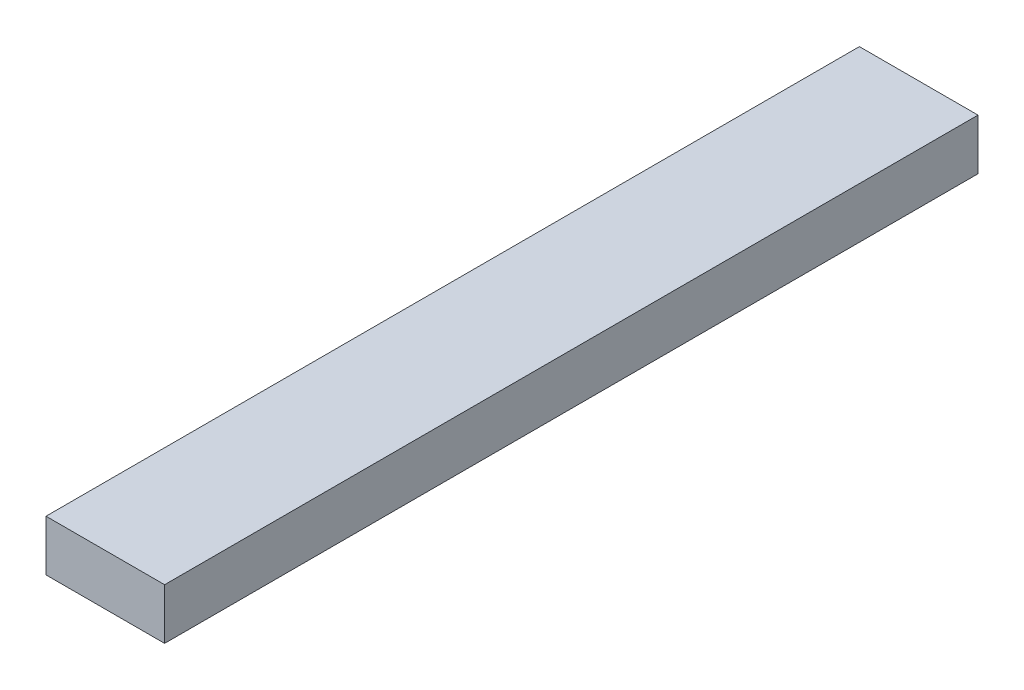
SolidWorks part; units mm, degrees
material "Pine"
ref_plane "Front Plane" through (0, 0, 0) normal (0, 0, 1) x (1, 0, 0)
ref_plane "Top Plane" through (0, 0, 0) normal (0, 1, 0) x (1, 0, 0)
ref_plane "Right Plane" through (0, 0, 0) normal (1, 0, 0) x (0, 0, -1)
sketch "Sketch1" plane through (0, 0, 0) normal (0, 0, 1) x (1, 0, 0)
  line L1 (0, 0) -> (88.9, 0)
  line L2 (0, 0) -> (0, 38.1)
  line L3 (0, 38.1) -> (88.9, 38.1)
  line L4 (88.9, 0) -> (88.9, 38.1)
  dimension "D1" = 88.9
  dimension "D2" = 38.1
extrude "Boss-Extrude1" add sketch "Sketch1" along normal blind 609.6
